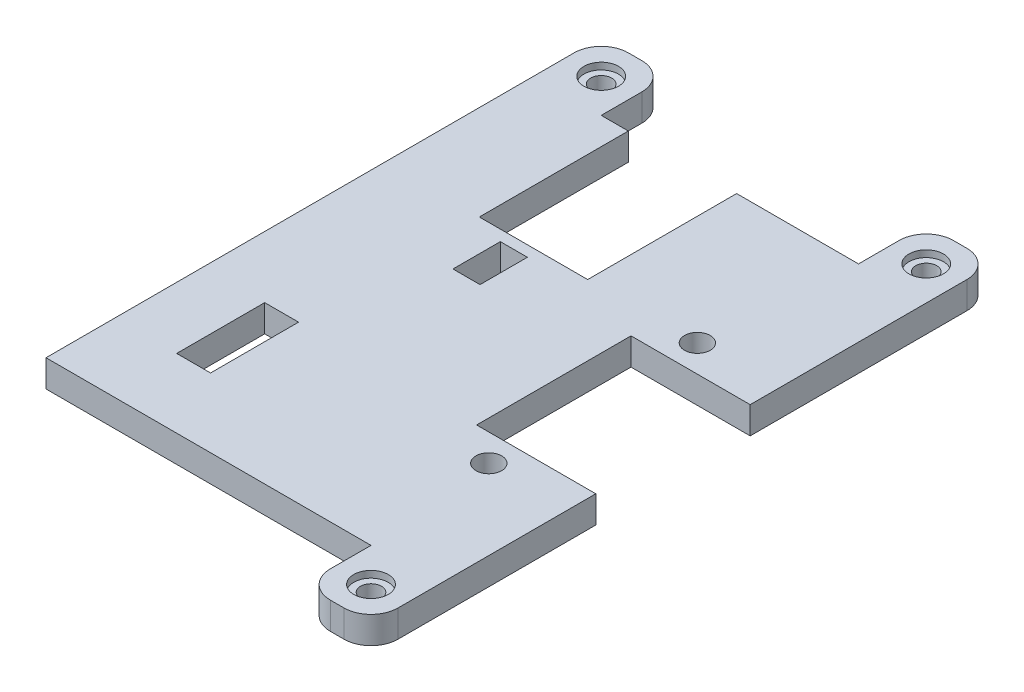
SolidWorks part; units mm, degrees
ref_plane "Спереди" through (0, 0, 0) normal (0, 0, 1) x (1, 0, 0)
ref_plane "Сверху" through (0, 0, 0) normal (0, 1, 0) x (1, 0, 0)
ref_plane "Справа" through (0, 0, 0) normal (1, 0, 0) x (0, 0, -1)
sketch "Sketch1" plane through (0, 0, 0) normal (0, 1, 0) x (1, 0, 0)
  line L0 (18.487, -44.731) -> (23.487, -44.731)
  line L1 (-5.513, 1.269) -> (-0.513, 1.269)
  line L2 (-5.513, 1.269) -> (-5.513, -39.731)
  line L4 (23.487, 1.269) -> (23.487, -44.731)
  line L6 (-0.513, 1.269) -> (-0.513, -3.731)
  line L7 (-0.513, -3.731) -> (18.487, -3.731)
  line L8 (18.487, 1.269) -> (18.487, -3.731)
  line L9 (-0.513, -39.731) -> (18.487, -39.731)
  line L12 (18.487, -39.731) -> (18.487, -44.731)
  line L13 (18.487, 1.269) -> (23.487, 1.269)
  line L14 (-0.513, -39.731) -> (-5.513, -39.731)
  circle A0 centre (-3.013, -1.231) radius 0.775
  circle A1 centre (20.987, -1.231) radius 0.775
  circle A2 centre (20.987, -42.231) radius 0.775
  point P2 (19.637, -42.2247)
  point P16 (14.2379, -29.4512)
  point P18 (20.7183, -29.9734)
  point P20 (0, 0)
  point P21 (20.987, -40.9999)
  dimension "D3" = 5
  dimension "D1" = 29
  dimension "D2" = 36
  dimension "D4" = 2.5
  dimension "D5" = 2.5
  dimension "D6" = 2.5
  dimension "D7" = 2.5
  dimension "D8" = 2.5
  dimension "D9" = 2.5
  dimension "D10" = 5
  dimension "D11" = 5
  dimension "D12" = 5
extrude "Boss-Extrude1" add sketch "Sketch1" along normal blind 2
sketch "Sketch2" plane through (0, 2, 0) normal (0, 1, 0) x (1, 0, 0)
  line L0 (-3.513, -39.731) -> (14.487, -39.731) construction
  line L1 (-5.513, -39.731) -> (18.487, -39.731) construction
  line L2 (5.487, -39.731) -> (5.487, -3.731) construction
  line L3 (18.487, -3.731) -> (-0.513, -3.731) construction
  line L4 (23.487, -44.731) -> (23.487, 1.269) construction
  line L5 (1.487, -3.731) -> (9.487, -3.731)
  line L6 (1.487, -3.731) -> (1.487, -14.731)
  line L7 (1.487, -14.731) -> (9.487, -14.731)
  line L8 (9.487, -3.731) -> (9.487, -14.731)
  line L9 (23.487, -16.731) -> (14.687, -16.731)
  line L10 (23.487, -16.731) -> (23.487, -28.131)
  line L11 (23.487, -28.131) -> (14.687, -28.131)
  line L12 (14.687, -16.731) -> (14.687, -28.131)
  line L14 (3.837, -15.531) -> (5.837, -15.531)
  line L15 (3.837, -15.531) -> (3.837, -19.031)
  line L16 (3.837, -19.031) -> (5.837, -19.031)
  line L17 (5.837, -15.531) -> (5.837, -19.031)
  line L18 (-0.963, -28.131) -> (1.537, -28.131)
  line L19 (-0.963, -28.131) -> (-0.963, -34.631)
  line L20 (-0.963, -34.631) -> (1.537, -34.631)
  line L21 (1.537, -28.131) -> (1.537, -34.631)
  circle A0 centre (17.587, -14.731) radius 0.95
  circle A1 centre (17.587, -30.131) radius 0.95
  dimension "D9" = 1.9
  dimension "D1" = 2
  dimension "D2" = 18
  dimension "D3" = 4
  dimension "D4" = 4
  dimension "D5" = 11
  dimension "D6" = 11.4
  dimension "D7" = 8.8
  dimension "D8" = 13
  dimension "D10" = 2
  dimension "D11" = 2
  dimension "D12" = 2.9
  dimension "D13" = 0.8
  dimension "D14" = 2.35
  dimension "D15" = 2
  dimension "D16" = 3.5
  dimension "D17" = 9.1
  dimension "D18" = 2.3
  dimension "D19" = 2.5
  dimension "D20" = 6.5
extrude "Cut-Extrude1" cut sketch "Sketch2" against normal through all
fillet "Fillet1" radius 2 6 edges at (18.487, 1, 44.731) (23.487, 1, 44.731) (23.487, 1, -1.269) (18.487, 1, -1.269) (-0.513, 1, -1.269) (-5.513, 1, -1.269)
sketch "Sketch3" plane through (0, 2, 0) normal (0, 1, 0) x (1, 0, 0)
  circle A0 centre (-3.013, -1.231) radius 1.275
  circle A1 centre (20.987, -1.231) radius 1.275
  circle A2 centre (20.987, -42.231) radius 1.275
  dimension "D1" = 2.55
extrude "Cut-Extrude2" cut sketch "Sketch3" against normal blind 0.5
